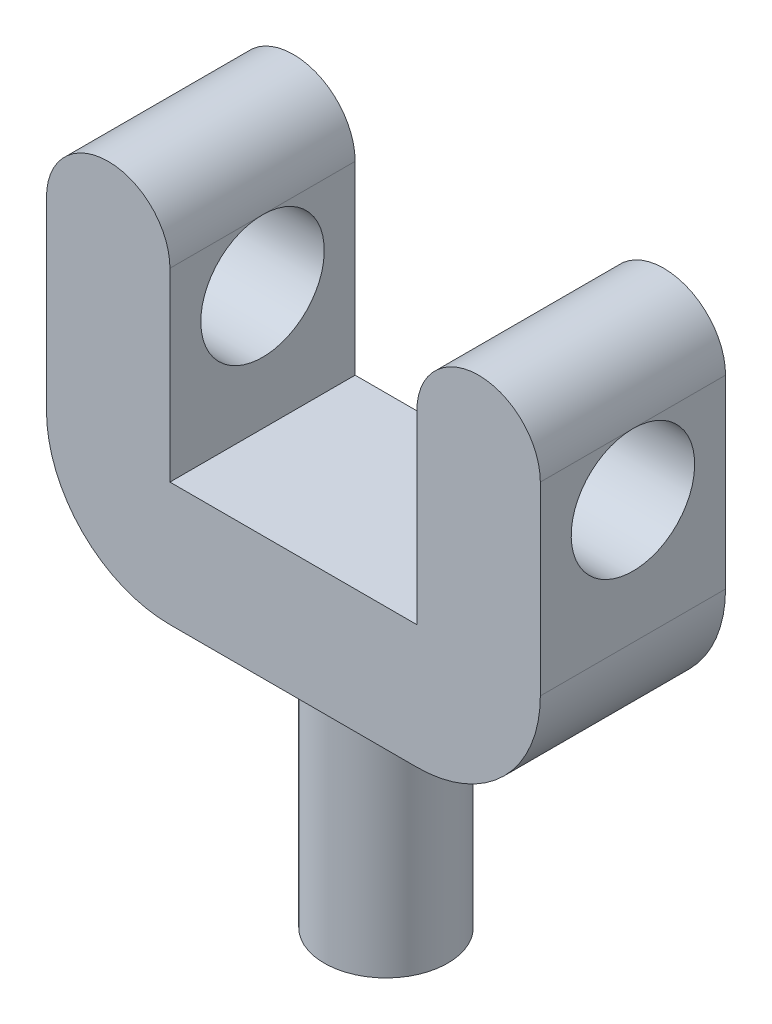
SolidWorks part; units mm, degrees
ref_plane "Front Plane" through (0, 0, 0) normal (0, 0, 1) x (1, 0, 0)
ref_plane "Top Plane" through (0, 0, 0) normal (0, 1, 0) x (1, 0, 0)
ref_plane "Right Plane" through (0, 0, 0) normal (1, 0, 0) x (0, 0, -1)
sketch "Sketch1" plane through (0, 0, 0) normal (0, 0, 1) x (1, 0, 0)
  line L0 (-15, 0) -> (15, 0) construction
  line L1 (-15, 0) -> (-15, 20) construction
  line L2 (15, 0) -> (15, 20) construction
  line L3 (10, 5) -> (10, 20)
  line L4 (-10, 5) -> (10, 5)
  line L5 (-10, 5) -> (-10, 20)
  line L6 (20, -5) -> (20, 20)
  line L7 (-20, -5) -> (20, -5)
  line L8 (-20, -5) -> (-20, 20)
  arc A0 (10, 20) -> (20, 20) centre (15, 20) cw
  arc A1 (-10, 20) -> (-20, 20) centre (-15, 20) ccw
  point P4 (0, 0)
  dimension "20" = 20
  dimension "D2" = 30
  dimension "D3" = 5
  dimension "D4" = 5
extrude "Boss-Extrude1" add sketch "Sketch1" along normal mid plane 15
sketch "Sketch2" plane through (20, 0, 0) normal (1, 0, 0) x (0, 0, -1)
  circle A0 centre (0, 15) radius 5
  dimension "D1" = 10
  dimension "D2" = 15
sketch "Sketch3" plane through (0, -5, 0) normal (0, -1, 0) x (1, 0, 0)
  circle A0 centre (0, 0) radius 5
  dimension "D1" = 10
extrude "Boss-Extrude2" add sketch "Sketch3" along normal blind 20
fillet "Fillet1" radius 10 2 edges at (-20, -5, 0) (20, -5, 0)
extrude "Cut-Extrude1" cut sketch "Sketch2" against normal up to surface (40 mm away) contours A0 up to face at (-20, 12.5, 0)
